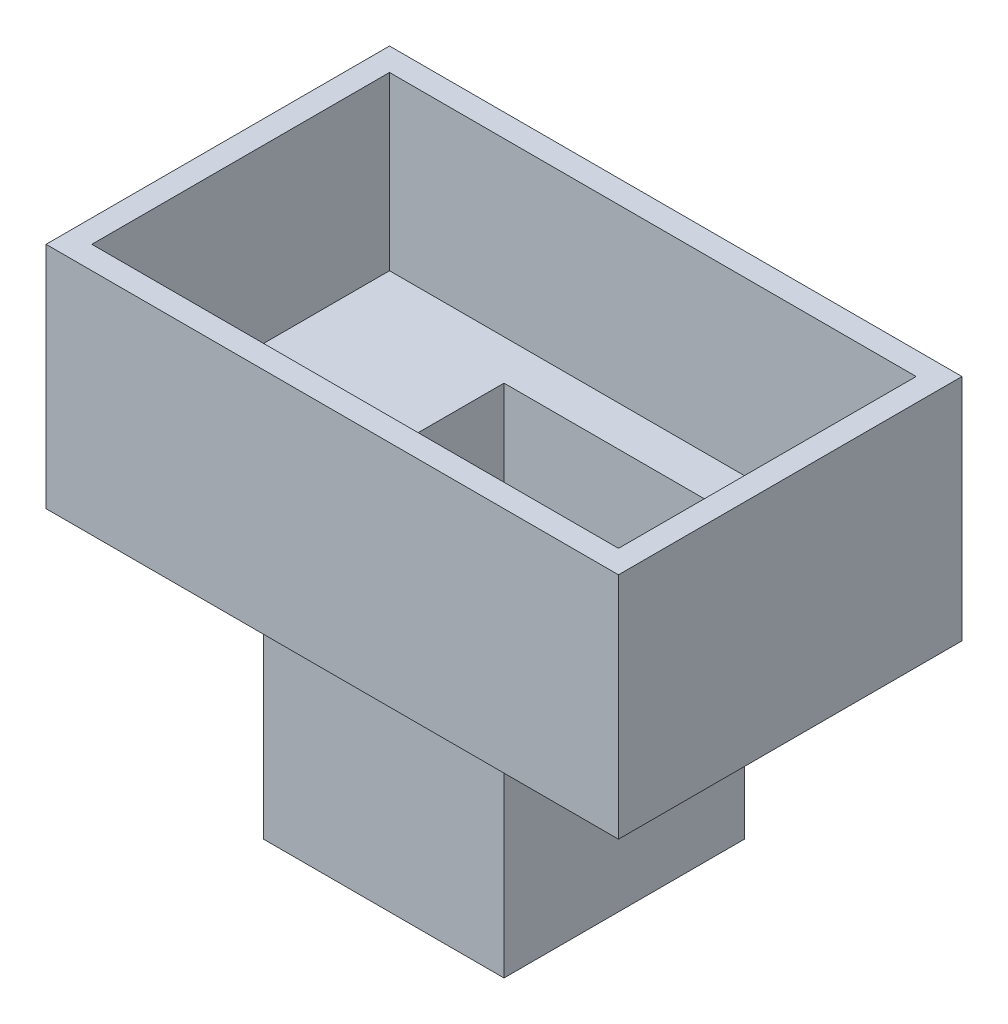
SolidWorks part; units mm, degrees
ref_plane "Front Plane" through (0, 0, 0) normal (0, 0, 1) x (1, 0, 0)
ref_plane "Top Plane" through (0, 0, 0) normal (0, 1, 0) x (1, 0, 0)
ref_plane "Right Plane" through (0, 0, 0) normal (1, 0, 0) x (0, 0, -1)
sketch "Sketch2" plane through (0, 0, 0) normal (0, 1, 0) x (1, 0, 0)
  line L1 (-9.7059, 7.6765) -> (11.2941, 7.6765)
  line L2 (-9.7059, 7.6765) -> (-9.7059, -13.3235)
  line L3 (-9.7059, -13.3235) -> (11.2941, -13.3235)
  line L4 (11.2941, 7.6765) -> (11.2941, -13.3235)
  dimension "D1" = 21
  dimension "D2" = 21
extrude "Boss-Extrude1" add sketch "Sketch2" along normal blind 20
sketch "Sketch3" plane through (0, 20, 0) normal (0, 1, 0) x (1, 0, 0)
  line L0 (-9.7059, -13.3235) -> (11.2941, -13.3235) construction
  line L1 (-8.7059, 6.6765) -> (10.2941, 6.6765)
  line L2 (-8.7059, 6.6765) -> (-8.7059, -12.3235)
  line L3 (-8.7059, -12.3235) -> (10.2941, -12.3235)
  line L4 (10.2941, 6.6765) -> (10.2941, -12.3235)
  line L5 (11.2941, -13.3235) -> (11.2941, 7.6765) construction
  line L6 (11.2941, 7.6765) -> (-9.7059, 7.6765) construction
  line L7 (-9.7059, 7.6765) -> (-9.7059, -13.3235) construction
  dimension "D1" = 1
  dimension "D2" = 1
  dimension "D3" = 1
  dimension "D4" = 1
extrude "Cut-Extrude1" cut sketch "Sketch3" against normal through all
sketch "Sketch4" plane through (0, 20, 0) normal (0, 1, 0) x (1, 0, 0)
  line L1 (-24.2059, 12.1765) -> (25.7941, 12.1765)
  line L2 (-24.2059, 12.1765) -> (-24.2059, -17.8235)
  line L3 (-24.2059, -17.8235) -> (25.7941, -17.8235)
  line L4 (25.7941, 12.1765) -> (25.7941, -17.8235)
  line L5 (-8.7059, -12.3235) -> (10.2941, -12.3235) construction
  line L8 (10.2941, -12.3235) -> (10.2941, 6.6765) construction
  point P6 (0.7941, -12.3235)
  point P11 (10.2941, -2.8235)
  dimension "D1" = 50
  dimension "D2" = 30
  dimension "D3" = 25
  dimension "D4" = 15
extrude "Boss-Extrude2" add sketch "Sketch4" along normal blind 20
sketch "Sketch5" plane through (0, 40, 0) normal (0, 1, 0) x (1, 0, 0)
  line L0 (25.7941, 12.1765) -> (-24.2059, 12.1765) construction
  line L1 (-22.2059, 10.1765) -> (23.7941, 10.1765)
  line L2 (-22.2059, 10.1765) -> (-22.2059, -15.8235)
  line L3 (-22.2059, -15.8235) -> (23.7941, -15.8235)
  line L4 (23.7941, 10.1765) -> (23.7941, -15.8235)
  line L5 (25.7941, -17.8235) -> (25.7941, 12.1765) construction
  line L7 (-24.2059, -17.8235) -> (25.7941, -17.8235) construction
  line L8 (-24.2059, 12.1765) -> (-24.2059, -17.8235) construction
  dimension "D1" = 2
  dimension "D2" = 2
  dimension "D3" = 2
  dimension "D4" = 2
extrude "Cut-Extrude2" cut sketch "Sketch5" against normal blind 15
sketch "Sketch6" plane through (0, 20, 0) normal (0, -1, 0) x (1, 0, 0)
  line L0 (10.2941, -6.6765) -> (-8.7059, -6.6765) construction
  line L1 (-8.7059, 12.3235) -> (10.2941, 12.3235)
  line L2 (-8.7059, 12.3235) -> (-8.7059, -6.6765)
  line L3 (-8.7059, -6.6765) -> (10.2941, -6.6765)
  line L4 (10.2941, 12.3235) -> (10.2941, -6.6765)
  line L5 (10.2941, -6.6765) -> (-8.7059, -6.6765) construction
extrude "Cut-Extrude3" cut sketch "Sketch6" against normal blind 15
